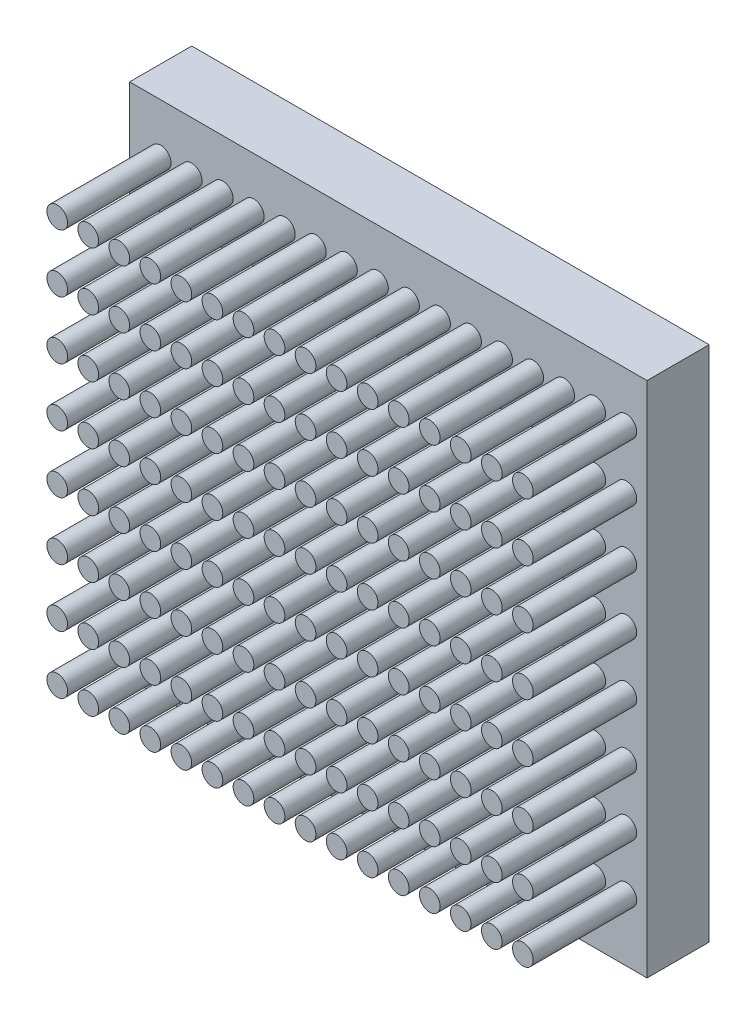
SolidWorks part; units mm, degrees
ref_plane "Front Plane" through (0, 0, 0) normal (0, 0, 1) x (1, 0, 0)
ref_plane "Top Plane" through (0, 0, 0) normal (0, 1, 0) x (1, 0, 0)
ref_plane "Right Plane" through (0, 0, 0) normal (1, 0, 0) x (0, 0, -1)
sketch "Sketch1" plane through (0, 0, 0) normal (0, 0, 1) x (1, 0, 0)
  line L1 (0, 0) -> (250, 0)
  line L2 (0, 0) -> (0, 250)
  line L3 (0, 250) -> (250, 250)
  line L4 (250, 0) -> (250, 250)
extrude "Boss-Extrude1" add sketch "Sketch1" along normal blind 30
sketch "Sketch2" plane through (0, 0, 30) normal (0, 0, 1) x (1, 0, 0)
  line L0 (0, 0) -> (0, 30)
  line L2 (0, 250) -> (0, 0) construction
  circle A0 centre (15, 30) radius 5
  circle A1 centre (30, 30) radius 5
  circle A2 centre (45, 30) radius 5
  circle A3 centre (60, 30) radius 5
  circle A4 centre (75, 30) radius 5
  circle A5 centre (90, 30) radius 5
  circle A6 centre (105, 30) radius 5
  circle A7 centre (120, 30) radius 5
  circle A8 centre (135, 30) radius 5
  circle A9 centre (150, 30) radius 5
  circle A10 centre (165, 30) radius 5
  circle A11 centre (180, 30) radius 5
  circle A12 centre (195, 30) radius 5
  circle A13 centre (210, 30) radius 5
  circle A14 centre (225, 30) radius 5
  circle A15 centre (240, 30) radius 5
  circle A16 centre (15, 58) radius 5
  circle A17 centre (30, 58) radius 5
  circle A18 centre (45, 58) radius 5
  circle A19 centre (60, 58) radius 5
  circle A20 centre (75, 58) radius 5
  circle A21 centre (90, 58) radius 5
  circle A22 centre (105, 58) radius 5
  circle A23 centre (120, 58) radius 5
  circle A24 centre (135, 58) radius 5
  circle A25 centre (150, 58) radius 5
  circle A26 centre (165, 58) radius 5
  circle A27 centre (180, 58) radius 5
  circle A28 centre (195, 58) radius 5
  circle A29 centre (210, 58) radius 5
  circle A30 centre (225, 58) radius 5
  circle A31 centre (240, 58) radius 5
  circle A32 centre (15, 86) radius 5
  circle A33 centre (30, 86) radius 5
  circle A34 centre (45, 86) radius 5
  circle A35 centre (60, 86) radius 5
  circle A36 centre (75, 86) radius 5
  circle A37 centre (90, 86) radius 5
  circle A38 centre (105, 86) radius 5
  circle A39 centre (120, 86) radius 5
  circle A40 centre (135, 86) radius 5
  circle A41 centre (150, 86) radius 5
  circle A42 centre (165, 86) radius 5
  circle A43 centre (180, 86) radius 5
  circle A44 centre (195, 86) radius 5
  circle A45 centre (210, 86) radius 5
  circle A46 centre (225, 86) radius 5
  circle A47 centre (240, 86) radius 5
  circle A48 centre (15, 114) radius 5
  circle A49 centre (30, 114) radius 5
  circle A50 centre (45, 114) radius 5
  circle A51 centre (60, 114) radius 5
  circle A52 centre (75, 114) radius 5
  circle A53 centre (90, 114) radius 5
  circle A54 centre (105, 114) radius 5
  circle A55 centre (120, 114) radius 5
  circle A56 centre (135, 114) radius 5
  circle A57 centre (150, 114) radius 5
  circle A58 centre (165, 114) radius 5
  circle A59 centre (180, 114) radius 5
  circle A60 centre (195, 114) radius 5
  circle A61 centre (210, 114) radius 5
  circle A62 centre (225, 114) radius 5
  circle A63 centre (240, 114) radius 5
  circle A64 centre (15, 142) radius 5
  circle A65 centre (30, 142) radius 5
  circle A66 centre (45, 142) radius 5
  circle A67 centre (60, 142) radius 5
  circle A68 centre (75, 142) radius 5
  circle A69 centre (90, 142) radius 5
  circle A70 centre (105, 142) radius 5
  circle A71 centre (120, 142) radius 5
  circle A72 centre (135, 142) radius 5
  circle A73 centre (150, 142) radius 5
  circle A74 centre (165, 142) radius 5
  circle A75 centre (180, 142) radius 5
  circle A76 centre (195, 142) radius 5
  circle A77 centre (210, 142) radius 5
  circle A78 centre (225, 142) radius 5
  circle A79 centre (240, 142) radius 5
  circle A80 centre (15, 170) radius 5
  circle A81 centre (30, 170) radius 5
  circle A82 centre (45, 170) radius 5
  circle A83 centre (60, 170) radius 5
  circle A84 centre (75, 170) radius 5
  circle A85 centre (90, 170) radius 5
  circle A86 centre (105, 170) radius 5
  circle A87 centre (120, 170) radius 5
  circle A88 centre (135, 170) radius 5
  circle A89 centre (150, 170) radius 5
  circle A90 centre (165, 170) radius 5
  circle A91 centre (180, 170) radius 5
  circle A92 centre (195, 170) radius 5
  circle A93 centre (210, 170) radius 5
  circle A94 centre (225, 170) radius 5
  circle A95 centre (240, 170) radius 5
  circle A96 centre (15, 198) radius 5
  circle A97 centre (30, 198) radius 5
  circle A98 centre (45, 198) radius 5
  circle A99 centre (60, 198) radius 5
  circle A100 centre (75, 198) radius 5
  circle A101 centre (90, 198) radius 5
  circle A102 centre (105, 198) radius 5
  circle A103 centre (120, 198) radius 5
  circle A104 centre (135, 198) radius 5
  circle A105 centre (150, 198) radius 5
  circle A106 centre (165, 198) radius 5
  circle A107 centre (180, 198) radius 5
  circle A108 centre (195, 198) radius 5
  circle A109 centre (210, 198) radius 5
  circle A110 centre (225, 198) radius 5
  circle A111 centre (240, 198) radius 5
  circle A112 centre (15, 226) radius 5
  circle A113 centre (30, 226) radius 5
  circle A114 centre (45, 226) radius 5
  circle A115 centre (60, 226) radius 5
  circle A116 centre (75, 226) radius 5
  circle A117 centre (90, 226) radius 5
  circle A118 centre (105, 226) radius 5
  circle A119 centre (120, 226) radius 5
  circle A120 centre (135, 226) radius 5
  circle A121 centre (150, 226) radius 5
  circle A122 centre (165, 226) radius 5
  circle A123 centre (180, 226) radius 5
  circle A124 centre (195, 226) radius 5
  circle A125 centre (210, 226) radius 5
  circle A126 centre (225, 226) radius 5
  circle A127 centre (240, 226) radius 5
  point P12 (0, 0)
  dimension "D1" = 15
  dimension "D2" = 16
extrude "Boss-Extrude2" add sketch "Sketch2" along normal blind 50 contours A3 | A0 | A1 | A2 | A4 | A5 | A6 | A7 | A8 | A9 | A10 | A11 | A12 | A13 | A14 | A15
pattern_linear "LPattern1" count 8 spacing 28 along (0, 1, 0) of "Boss-Extrude2"
